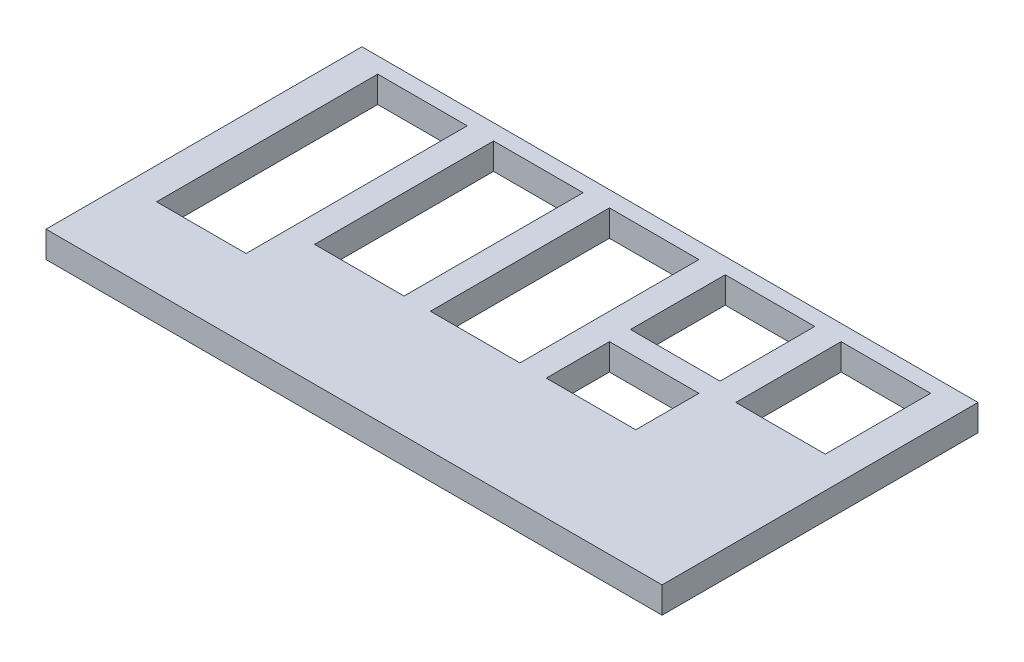
SolidWorks part; units mm, degrees
ref_plane "Front" through (0, 0, 0) normal (0, 0, 1) x (1, 0, 0)
ref_plane "Top" through (0, 0, 0) normal (0, 1, 0) x (1, 0, 0)
ref_plane "Right" through (0, 0, 0) normal (1, 0, 0) x (0, 0, -1)
sketch "Sketch1" plane through (0, 0, 0) normal (0, 1, 0) x (1, 0, 0)
  line L1 (-58.5, -30) -> (58.5, -30)
  line L2 (-58.5, -30) -> (-58.5, 30)
  line L3 (-58.5, 30) -> (58.5, 30)
  line L4 (58.5, -30) -> (58.5, 30)
  line L5 (-58.5, -30) -> (58.5, 30) construction
  line L6 (-58.5, 30) -> (58.5, -30) construction
  line L12 (13.5, 9) -> (30.5, 9)
  line L13 (-52.5, -15) -> (-35.5, -15)
  line L14 (-52.5, -15) -> (-52.5, 27)
  line L15 (-52.5, 27) -> (-35.5, 27)
  line L16 (-35.5, -15) -> (-35.5, 27)
  line L17 (-52.5, -15) -> (-35.5, 27) construction
  line L18 (-52.5, 27) -> (-35.5, -15) construction
  line L23 (13.5, 9) -> (13.5, 27)
  line L24 (13.5, 27) -> (30.5, 27)
  line L25 (-13.5, 27) -> (-30.5, 27)
  line L26 (-13.5, 27) -> (-13.5, -7)
  line L27 (-13.5, -7) -> (-30.5, -7)
  line L28 (-30.5, 27) -> (-30.5, -7)
  line L29 (-13.5, 27) -> (-30.5, -7) construction
  line L30 (-13.5, -7) -> (-30.5, 27) construction
  line L35 (30.5, 9) -> (30.5, 27)
  line L36 (13.5, 9) -> (30.5, 27) construction
  line L37 (-8.5, -7) -> (8.5, -7)
  line L38 (-8.5, -7) -> (-8.5, 27)
  line L39 (-8.5, 27) -> (8.5, 27)
  line L40 (8.5, -7) -> (8.5, 27)
  line L41 (-8.5, -7) -> (8.5, 27) construction
  line L42 (-8.5, 27) -> (8.5, -7) construction
  line L48 (13.5, 27) -> (30.5, 9) construction
  line L49 (35.5, 7) -> (52.5, 7)
  line L50 (35.5, 7) -> (35.5, 27)
  line L51 (35.5, 27) -> (52.5, 27)
  line L52 (52.5, 7) -> (52.5, 27)
  line L53 (35.5, 7) -> (52.5, 27) construction
  line L54 (35.5, 27) -> (52.5, 7) construction
  line L55 (13.5, 5) -> (30.5, 5)
  line L56 (13.5, 5) -> (13.5, -7)
  line L57 (13.5, -7) -> (30.5, -7)
  line L58 (30.5, 5) -> (30.5, -7)
  line L59 (13.5, 5) -> (30.5, -7) construction
  line L60 (13.5, -7) -> (30.5, 5) construction
  line L67 (-58.5, -30) -> (58.5, -30)
  point P0 (0, 0)
  point P6 (44, 17)
  point P9 (22, 18)
  point P11 (-44, 6)
  point P21 (-22, 10)
  point P26 (22, -1)
  point P31 (0, 10)
  dimension "D1" = 117
  dimension "D2" = 60
  dimension "D3" = 6
  dimension "D4" = 3
  dimension "D5" = 17
  dimension "D6" = 5
  dimension "D7" = 17
  dimension "D8" = 3
  dimension "D9" = 5
  dimension "D10" = 3
  dimension "D11" = 17
  dimension "D12" = 5
  dimension "D13" = 17
  dimension "D14" = 18
  dimension "D15" = 5
  dimension "D16" = 17
  dimension "D17" = 20
  dimension "D18" = 12
  dimension "D19" = 6
  dimension "D21" = 42
  dimension "D22" = 34
  dimension "D23" = 4
  dimension "D25" = 34
extrude "Boss-Extrude1" add sketch "Sketch1" along normal blind 5
